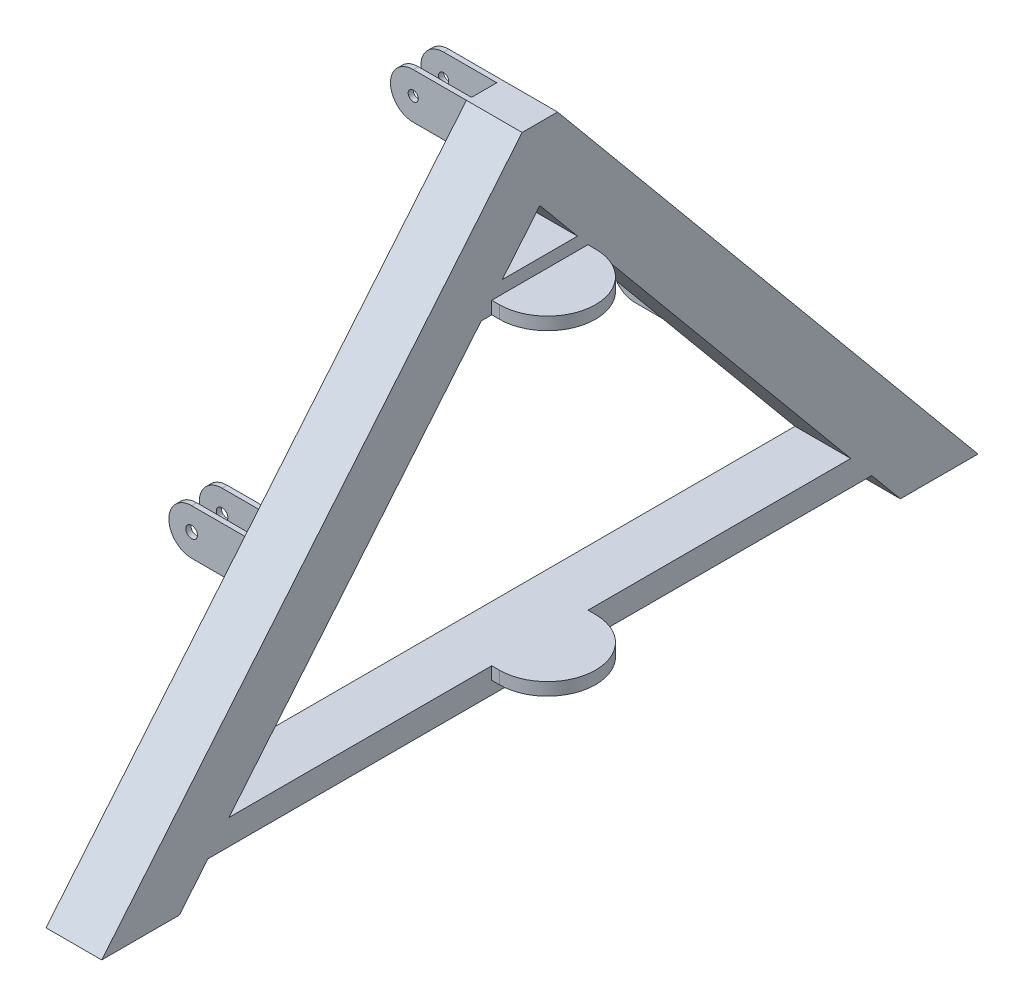
SolidWorks part; units mm, degrees
other "Markup1"
sketch "Sketch7" plane through (-150, 547, -482.5) normal (-0.7837, 0.5348, -0.3159) x (-0.4255, -0.0917, 0.9003)
material "AISI 4340 Steel, normalized"
ref_plane "Front Plane" through (0, 0, 0) normal (0, 0, 1) x (1, 0, 0)
ref_plane "Top Plane" through (0, 0, 0) normal (0, 1, 0) x (1, 0, 0)
ref_plane "Right Plane" through (0, 0, 0) normal (1, 0, 0) x (0, 0, -1)
sketch "Sketch1" plane through (0, 0, 0) normal (1, 0, 0) x (0, 0, -1)
  line L0 (-462.5, 0) -> (-412.5, 0)
  line L1 (0, -179.0012) -> (0, 585.1654) construction
  line L2 (-327.5, 0) -> (-327.5, 10)
  line L3 (-327.5, 10) -> (-472.5, 10)
  line L4 (-472.5, 10) -> (-472.5, -80)
  line L6 (-472.5, -80) -> (-462.5, -80)
  line L7 (-462.5, -80) -> (-462.5, 0)
  line L8 (-412.5, 0) -> (-412.5, -80)
  line L9 (-412.5, -80) -> (-402.5, -80)
  line L10 (-402.5, -80) -> (-402.5, 0)
  line L11 (-402.5, 0) -> (-327.5, 0)
  line L12 (25, 457) -> (-25, 457)
  line L13 (-101.4137, 457) -> (-101.4137, 447)
  line L14 (-101.4137, 447) -> (101.4137, 447)
  line L15 (-35, 457) -> (-35, 537)
  line L16 (-35, 537) -> (-25, 537)
  line L17 (-25, 537) -> (-25, 457)
  line L18 (-35, 457) -> (-101.4137, 457)
  line L19 (35, 457) -> (101.4137, 457)
  line L20 (25, 537) -> (25, 457)
  line L21 (35, 537) -> (25, 537)
  line L22 (35, 457) -> (35, 537)
  line L23 (101.4137, 457) -> (101.4137, 447)
  line L24 (402.5, 0) -> (327.5, 0)
  line L25 (402.5, -80) -> (402.5, 0)
  line L26 (412.5, -80) -> (402.5, -80)
  line L27 (412.5, 0) -> (412.5, -80)
  line L28 (462.5, -80) -> (462.5, 0)
  line L29 (472.5, -80) -> (462.5, -80)
  line L30 (472.5, 10) -> (472.5, -80)
  line L31 (327.5, 10) -> (472.5, 10)
  line L32 (327.5, 0) -> (327.5, 10)
  line L33 (462.5, 0) -> (412.5, 0)
  line L34 (-472.5, 10) -> (-35, 537) construction
  point P16 (0, 457)
  point P27 (0, 447)
  dimension "D1" = 655
  dimension "D2" = 10
  dimension "D3" = 825
  dimension "D4" = 50
  dimension "D5" = 437
  dimension "D6" = 10
  dimension "D7" = 90
  dimension "D8" = 90
  dimension "D9" = 50
extrude "Boss-Extrude1" add sketch "Sketch1" along normal blind 100
sketch "Sketch2" plane through (0, 0, 0) normal (-1, 0, 0) x (0, 0, 1)
  line L0 (-472.5, -80) -> (-472.5, 10)
  line L1 (-472.5, 10) -> (-462.5, 10)
  line L2 (-472.5, 10) -> (-327.5, 10) construction
  line L3 (-462.5, 10) -> (-462.5, -80)
  line L4 (-462.5, -80) -> (-472.5, -80)
  line L5 (-462.5, 0) -> (-462.5, -80) construction
  line L6 (-412.5, -80) -> (-402.5, -80)
  line L7 (-402.5, -80) -> (-402.5, 10)
  line L8 (-402.5, 10) -> (-412.5, 10)
  line L9 (-412.5, 10) -> (-412.5, -80)
  line L10 (0, 0) -> (0, 241.8238) construction
  line L11 (-35, 537) -> (-25, 537)
  line L12 (-25, 537) -> (-25, 447)
  line L13 (101.4137, 447) -> (-101.4137, 447) construction
  line L14 (-25, 447) -> (-35, 447)
  line L15 (-35, 447) -> (-35, 537)
  line L16 (35, 447) -> (35, 537)
  line L17 (25, 447) -> (35, 447)
  line L18 (25, 537) -> (25, 447)
  line L19 (35, 537) -> (25, 537)
  line L20 (412.5, 10) -> (412.5, -80)
  line L21 (402.5, 10) -> (412.5, 10)
  line L22 (402.5, -80) -> (402.5, 10)
  line L23 (412.5, -80) -> (402.5, -80)
  line L24 (462.5, -80) -> (472.5, -80)
  line L25 (462.5, 10) -> (462.5, -80)
  line L26 (472.5, 10) -> (462.5, 10)
  line L27 (472.5, -80) -> (472.5, 10)
extrude "Boss-Extrude2" add sketch "Sketch2" along normal blind 150
sketch "Sketch3" plane through (100, 0, 0) normal (1, 0, 0) x (0, 0, -1)
  line L0 (0, 0) -> (0, 159.5705) construction
  line L3 (-472.5, 10) -> (-35, 537)
  line L4 (-35, 537) -> (35, 537)
  line L5 (-327.5, 0) -> (0, 394.4971)
  line L8 (327.5, 0) -> (0, 394.4971)
  line L9 (472.5, 10) -> (35, 537)
  line L18 (-327.5, 0) -> (-711.8691, -463)
  line L22 (-472.5, 10) -> (-865.1708, -463)
  line L23 (-865.1708, -463) -> (-711.8691, -463)
  line L24 (472.5, 10) -> (865.1708, -463)
  line L25 (865.1708, -463) -> (711.8691, -463)
  line L26 (327.5, 0) -> (711.8691, -463)
  point P1 (-861.6747, -643.4516)
  point P16 (-414.4661, -104.7569)
  point P18 (0, 537)
  point P19 (-435.0198, -129.5153)
  point P20 (0, 0)
  point P21 (-703.5674, -465.387)
  dimension "D1" = 1000
extrude "Boss-Extrude3" add sketch "Sketch3" along normal blind 10
sketch "Sketch4" plane through (0, 0, 472.5) normal (0, 0, 1) x (1, 0, 0)
  line L0 (100, 10) -> (-150, 10) construction
  line L1 (-150, -80) -> (-150, 10) construction
  line L2 (110, -80) -> (-150, -80) construction
  line L3 (-105, 10) -> (-150, 10)
  line L4 (-150, 10) -> (-150, -80)
  line L5 (-150, -80) -> (-105, -80)
  line L6 (100, 537) -> (-150, 537) construction
  line L7 (-150, 447) -> (0, 447) construction
  line L8 (-150, 447) -> (-150, 537) construction
  line L9 (-105, 447) -> (-150, 447)
  line L10 (-150, 447) -> (-150, 537)
  line L11 (-150, 537) -> (-105, 537)
  arc A0 (-105, 10) -> (-105, -80) centre (-105, -35) ccw
  circle A1 centre (-105, -35) radius 11.5
  arc A2 (-105, 537) -> (-105, 447) centre (-105, 492) ccw
  circle A3 centre (-105, 492) radius 10
  dimension "D1" = 23
  dimension "D2" = 20
extrude "Cut-Extrude2" cut sketch "Sketch4" against normal through all and the other way through all
sketch "Sketch5" plane through (100, 0, 0) normal (-1, 0, 0) x (0, 0, 1)
  line L1 (-865.1708, -463) -> (-472.5, 10) construction
  line L2 (-711.8691, -463) -> (-865.1708, -463) construction
  line L5 (-327.5, 0) -> (-711.8691, -463) construction
  line L7 (-865.1708, -463) -> (-35, 537)
  line L8 (-35, 537) -> (35, 537) construction
  line L10 (0, 0) -> (0, 90.9908) construction
  line L11 (-711.8691, -463) -> (0, 394.4971)
  line L15 (-843.8722, -453) -> (-716.5642, -453)
  line L16 (-843.8722, -453) -> (-30.3048, 527)
  line L17 (-865.1708, -463) -> (-711.8691, -463)
  line L18 (716.5642, -453) -> (0, 410.1528)
  line L19 (-716.5642, -453) -> (0, 410.1528)
  line L20 (865.1708, -463) -> (711.8691, -463)
  line L23 (35, 537) -> (-35, 537)
  line L33 (30.3048, 527) -> (-30.3048, 527)
  line L34 (-25, 537) -> (25, 537) construction
  line L36 (843.8722, -453) -> (30.3048, 527)
  line L37 (843.8722, -453) -> (716.5642, -453)
  line L38 (711.8691, -463) -> (0, 394.4971)
  line L39 (865.1708, -463) -> (35, 537)
  point P6 (0, 537.3228)
  point P7 (0, 547)
  point P9 (0, 527)
  point P12 (0, 537)
  dimension "D1" = 10
  dimension "D2" = 10
  dimension "D3" = 10
  dimension "D4" = 10
extrude "Boss-Extrude4" add sketch "Sketch5" along normal blind 100
sketch "Sketch8" plane through (0, 0, 0) normal (-1, 0, 0) x (0, 0, 1)
  line L0 (-472.5, 10) -> (-865.1708, -463)
  line L1 (-865.1708, -463) -> (-711.8691, -463)
  line L2 (-711.8691, -463) -> (0, 394.4971)
  line L3 (0, 394.4971) -> (711.8691, -463)
  line L4 (711.8691, -463) -> (865.1708, -463)
  line L5 (865.1708, -463) -> (472.5, 10)
  line L6 (472.5, 10) -> (35, 537)
  line L7 (35, 537) -> (-35, 537)
  line L8 (-35, 537) -> (-472.5, 10)
  line L9 (-865.1708, -463) -> (-711.8691, -463) construction
  line L10 (-711.8691, -463) -> (0, 394.4971) construction
  line L11 (25, 537) -> (-25, 537) construction
  point P4 (701.7504, 20)
  point P19 (703.5674, -453)
  point P21 (828.5727, 20)
  point P22 (875.1708, -453)
  point P24 (-703.5674, -453)
  point P29 (-875.1708, -453)
extrude "Boss-Extrude5" add sketch "Sketch8" against normal blind 10
sketch "Sketch11" plane through (110, 0, 0) normal (1, 0, 0) x (0, 0, -1)
  line L0 (-95, 255.0629) -> (95, 255.0629)
  line L1 (-711.8691, -463) -> (0, 394.4971) construction
  line L2 (-95, 255.0629) -> (-95, 280.0629)
  line L3 (-95, 280.0629) -> (95, 280.0629)
  line L4 (95, 280.0629) -> (95, 255.0629)
  line L5 (-95, -344.9371) -> (95, -344.9371)
  line L6 (-95, -344.9371) -> (-95, -369.9371)
  line L7 (-95, -369.9371) -> (95, -369.9371)
  line L8 (95, -369.9371) -> (95, -344.9371)
  point P4 (0, 280.0629)
  dimension "D1" = 190
  dimension "D2" = 25
  dimension "D3" = 600
  dimension "D4" = 25
extrude "Boss-Extrude7" add sketch "Sketch11" along normal mid plane 220
sketch "Sketch13" plane through (110, 0, 0) normal (1, 0, 0) x (0, 0, -1)
  line L0 (74.2457, 305.0629) -> (-74.2457, 305.0629)
  line L2 (-711.8691, -463) -> (0, 394.4971) construction
  line L3 (0, 394.4971) -> (711.8691, -463) construction
  line L4 (-613.8567, -344.9371) -> (613.8567, -344.9371)
  line L7 (-613.8567, -344.9371) -> (-655.3653, -394.9371)
  line L8 (-655.3653, -394.9371) -> (655.3653, -394.9371)
  line L9 (655.3653, -394.9371) -> (613.8567, -344.9371)
  line L10 (-74.2457, 305.0629) -> (-115.7543, 255.0629)
  line L11 (-115.7543, 255.0629) -> (115.7543, 255.0629)
  line L12 (115.7543, 255.0629) -> (74.2457, 305.0629)
  line L14 (95, -344.9371) -> (-95, -344.9371) construction
  line L15 (-95, 255.0629) -> (95, 255.0629) construction
  dimension "D1" = 50
extrude "Boss-Extrude11" add sketch "Sketch13" against normal blind 110
sketch "Sketch12" plane through (0, 280.0629, 0) normal (0, 1, 0) x (1, 0, 0)
  line L0 (220, 95) -> (110, 95) construction
  line L2 (220, -95) -> (110, -95) construction
  line L3 (220, 95) -> (220, -95) construction
  line L4 (125, 95) -> (220, 95)
  line L5 (220, 95) -> (220, -95)
  line L6 (220, -95) -> (125, -95)
  arc A0 (125, -95) -> (125, 95) centre (125, 0) ccw
  line M3 (110, -95) -> (220, -95)
  line M4 (220, -95) -> (220, 95)
  line M5 (220, 95) -> (110, 95)
extrude "Cut-Extrude4" cut sketch "Sketch12" against normal through all contours A0 L5 M5 | A0 M3 M4
sketch "Sketch14" plane through (0, 0, 0) normal (-1, 0, 0) x (0, 0, 1)
  line L0 (-634.0667, -384.9371) -> (634.0667, -384.9371)
  line L1 (634.0667, -384.9371) -> (609.1616, -354.9371)
  line L2 (609.1616, -354.9371) -> (-609.1616, -354.9371)
  line L3 (-609.1616, -354.9371) -> (-634.0667, -384.9371)
  line L4 (655.3653, -394.9371) -> (-655.3653, -394.9371) construction
  line L5 (-613.8567, -344.9371) -> (613.8567, -344.9371) construction
  line L12 (-694.1603, -441.6685) -> (-504.9999, -213.8113) construction
  line L15 (-711.8691, -463) -> (-655.3653, -394.9371) construction
  line L16 (437.5839, -132.604) -> (518.5444, -230.1266) construction
  line L17 (115.7543, 255.0629) -> (613.8567, -344.9371) construction
  line L18 (-94.4557, 265.0629) -> (94.4557, 265.0629)
  line L19 (94.4557, 265.0629) -> (69.5506, 295.0629)
  line L20 (69.5506, 295.0629) -> (-69.5506, 295.0629)
  line L21 (-69.5506, 295.0629) -> (-94.4557, 265.0629)
  line L22 (115.7543, 255.0629) -> (-115.7543, 255.0629) construction
  line L23 (-74.2457, 305.0629) -> (74.2457, 305.0629) construction
  dimension "D1" = 10
  dimension "D2" = 10
  dimension "D3" = 10
  dimension "D4" = 10
  dimension "D5" = 10
  dimension "D6" = 10
  dimension "D7" = 10
  dimension "D8" = 10
ref_plane "Plane1" through (55, 0, 0) normal (-1, 0, 0) x (0, 0, 1)
extrude "Cut-Extrude5" cut sketch "Sketch14" against normal mid plane 90 from surface at -55 starting at plane "Plane1"
